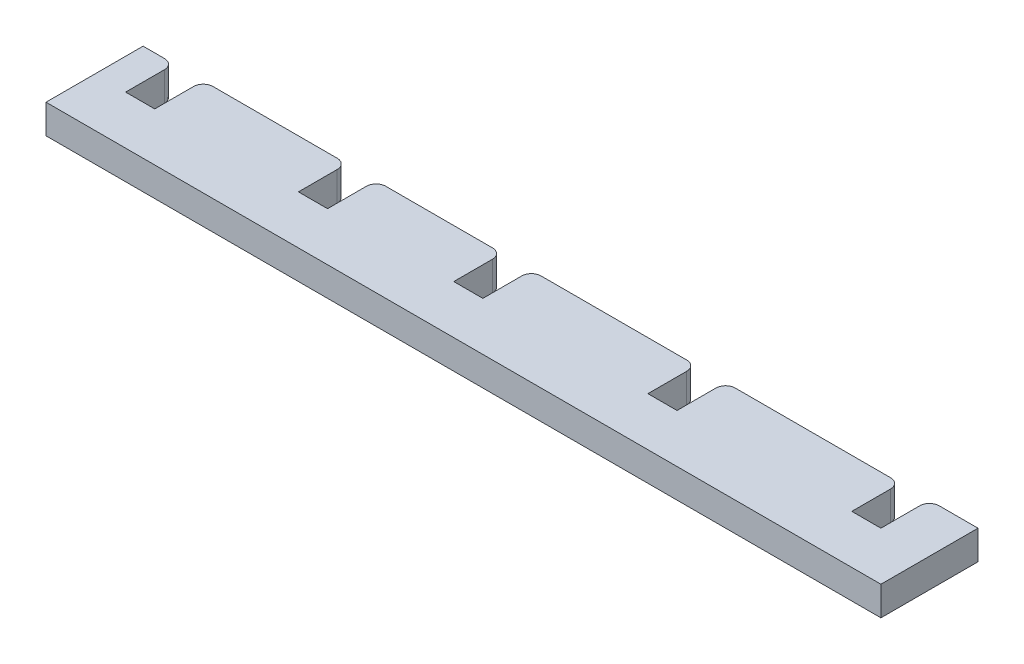
SolidWorks part; units mm, degrees
ref_plane "Front Plane" through (0, 0, 0) normal (0, 0, 1) x (1, 0, 0)
ref_plane "Top Plane" through (0, 0, 0) normal (0, 1, 0) x (1, 0, 0)
ref_plane "Right Plane" through (0, 0, 0) normal (1, 0, 0) x (0, 0, -1)
sketch "Sketch1" plane through (0, 0, 0) normal (0, 0, 1) x (1, 0, 0)
  line L1 (0, 0) -> (86, 0)
  line L2 (0, 0) -> (0, 3)
  line L3 (0, 3) -> (86, 3)
  line L4 (86, 0) -> (86, 3)
  dimension "D1" = 3
  dimension "D2" = 86
extrude "Boss-Extrude1" add sketch "Sketch1" along normal blind 10
sketch "Sketch3" plane through (0, 0, 0) normal (0, 0, -1) x (-1, 0, 0)
  line L0 (0, 0) -> (-86, 0) construction
  line L4 (-81, 3) -> (-81, 0)
  line L5 (-86, 3) -> (0, 3) construction
  line L7 (-78, 3) -> (-78, 0)
  line L9 (-60, 3) -> (-60, 0)
  line L10 (-81, 3) -> (-78, 3)
  line L12 (-57, 3) -> (-57, 0)
  line L14 (-40, 3) -> (-40, 0)
  line L16 (-37, 3) -> (-37, 0)
  line L18 (-24, 3) -> (-24, 0)
  line L20 (-21, 3) -> (-21, 0)
  line L22 (-6.2, 3) -> (-6.2, 0)
  line L24 (-3.2, 3) -> (-3.2, 0)
  line L27 (-3.2, 0) -> (-6.2, 0)
  line L28 (-78, 0) -> (-81, 0)
  line L29 (-60, 3) -> (-57, 3)
  line L30 (-40, 3) -> (-37, 3)
  line L31 (-57, 0) -> (-60, 0)
  line L32 (-37, 0) -> (-40, 0)
  line L33 (-24, 3) -> (-21, 3)
  line L34 (-6.2, 3) -> (-3.2, 3)
  line L35 (-21, 0) -> (-24, 0)
  line L37 (-86, 0) -> (-86, 3) construction
  dimension "D2" = 3
  dimension "D3" = 18
  dimension "D4" = 3
  dimension "D5" = 17
  dimension "D6" = 3
  dimension "D7" = 13
  dimension "D8" = 3
  dimension "D9" = 14.8
  dimension "D10" = 3
  dimension "D11" = 5
extrude "Cut-Extrude2" cut sketch "Sketch3" against normal blind 5
fillet "Fillet2" radius 1 10 edges at (3.2, 1.5, 0) (6.2, 1.5, 0) (21, 1.5, 0) (24, 1.5, 0) (37, 1.5, 0) (40, 1.5, 0) (57, 1.5, 0) (60, 1.5, 0) (78, 1.5, 0) (81, 1.5, 0)
